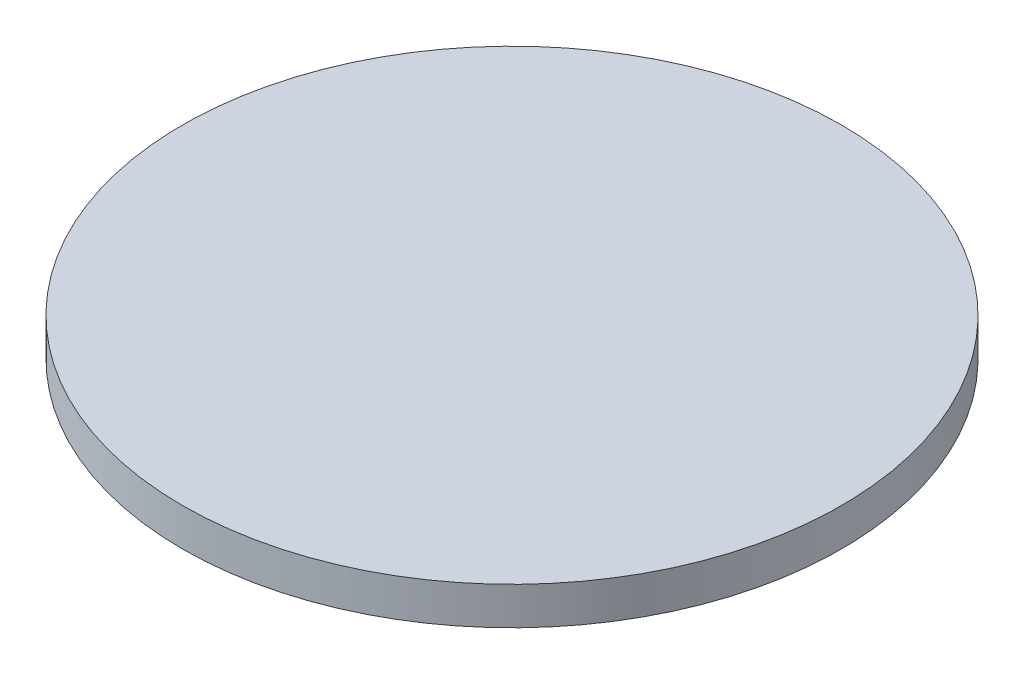
SolidWorks part; units mm, degrees
ref_plane "Front Plane" through (0, 0, 0) normal (0, 0, 1) x (1, 0, 0)
ref_plane "Top Plane" through (0, 0, 0) normal (0, 1, 0) x (1, 0, 0)
ref_plane "Right Plane" through (0, 0, 0) normal (1, 0, 0) x (0, 0, -1)
sketch "Sketch1" plane through (0, 0, 0) normal (0, 1, 0) x (1, 0, 0)
  circle A0 centre (0, 0) radius 22.225
  dimension "D1" = 44.45
extrude "Boss-Extrude1" add sketch "Sketch1" along normal blind 2.54
